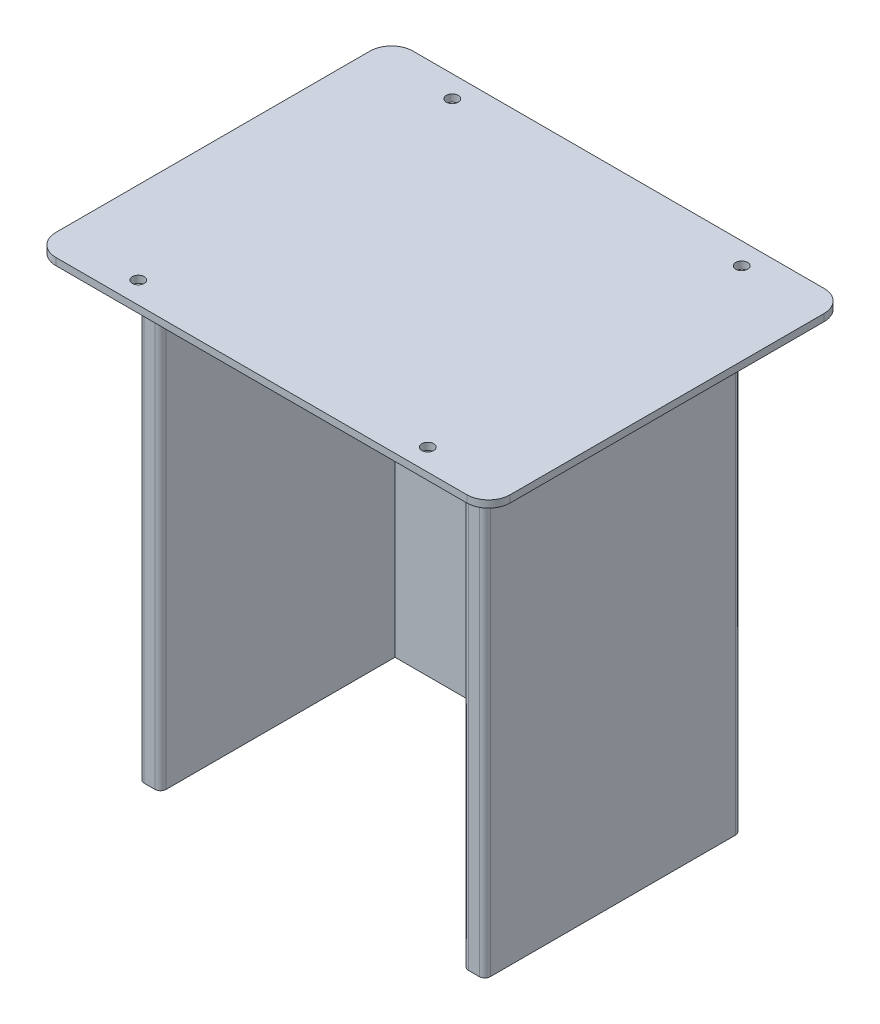
SolidWorks part; units mm, degrees
ref_plane "Front Plane" through (0, 0, 0) normal (0, 0, 1) x (1, 0, 0)
ref_plane "Top Plane" through (0, 0, 0) normal (0, 1, 0) x (1, 0, 0)
ref_plane "Right Plane" through (0, 0, 0) normal (1, 0, 0) x (0, 0, -1)
sketch "Sketch1" plane through (0, 0, 0) normal (0, 1, 0) x (1, 0, 0)
  line L1 (-99.9344, -82.55) -> (110.0102, -82.55)
  line L2 (-99.9344, -82.55) -> (-99.9344, 82.55)
  line L3 (-99.9344, 82.55) -> (110.0102, 82.55)
  line L4 (110.0102, -82.55) -> (110.0102, 82.55)
  point P0 (0, 0)
  dimension "D1" = 165.1
  dimension "D2" = 99.9344
  dimension "D3" = 82.55
  dimension "D4" = 209.9446
extrude "Boss-Extrude1" add sketch "Sketch1" along normal blind 3.302
hole_wizard "M5 Clearance Hole2" positions "Sketch10" profile "Sketch11" hole size "M5" standard "ANSI Metric" end condition up to next
sketch "Sketch10" plane through (0, 3.302, 0) normal (0, 1, 0) x (1, 0, 0)
  line L0 (5.0379, -82.55) -> (5.0379, 82.55) construction
  line L1 (-99.9344, -82.55) -> (110.0102, -82.55) construction
  line L2 (110.0102, 82.55) -> (-99.9344, 82.55) construction
  line L5 (100.0102, -72.55) -> (-89.9344, -72.55) construction
  line L6 (100.0102, -72.55) -> (100.0102, 72.55) construction
  line L7 (100.0102, 72.55) -> (-89.9344, 72.55) construction
  line L8 (-89.9344, -72.55) -> (-89.9344, 72.55) construction
  line L9 (100.0102, -72.55) -> (-89.9344, 72.55) construction
  line L10 (100.0102, 72.55) -> (-89.9344, -72.55) construction
  line L11 (110.0102, -82.55) -> (110.0102, 82.55) construction
  line L12 (-99.9344, 82.55) -> (-99.9344, -82.55) construction
  point P0 (71.9102, -72.55)
  point P7 (-61.8344, -72.55)
  point P9 (71.9102, 72.55)
  point P16 (-61.8344, 72.55)
  point P197 (71.8682, 72.55)
  point P198 (71.8682, 72.55)
  point P199 (0, 0)
  point P200 (0, 0)
  point P201 (0, 0)
  point P202 (0, 0)
  point P203 (0, 0)
  point P204 (0, 0)
  point P205 (0, 0)
  point P206 (0, 0)
  point P209 (0, 0)
  point P210 (0, 0)
  point P211 (0, 0)
  point P212 (0, 0)
  point P213 (0, 0)
  dimension "D1" = 10
  dimension "D2" = 10
  dimension "D3" = 10
  dimension "D4" = 38.1
  dimension "D5" = 38.1
  dimension "D6" = 10
sketch "Sketch11" plane through (71.9102, 3.302, 72.55) normal (1, 0, 0) x (0, 0, 1)
  line L0 (0, 0) -> (0, 3.302)
  line L1 (0, 3.302) -> (2.75, 3.302)
  line L2 (2.75, 3.302) -> (2.75, 0)
  line L5 (2.75, 0) -> (0, 0)
  line L11 (0, -6.35) -> (0, 107.95) construction
  dimension "Thru Hole Dia." = 5.5
  dimension "Thru Hole Depth" = 3.302
sketch "Sketch12" plane through (0, 0, 0) normal (0, -1, 0) x (1, 0, 0)
  line L0 (0, 82.55) -> (0, 59.25) construction
  line L2 (-99.9344, 0) -> (-70.043, 0) construction
  line L3 (-99.9344, -82.55) -> (-99.9344, 82.55) construction
  line L4 (0, -82.55) -> (0, -59.25) construction
  line L6 (-75.0051, 80.5434) -> (-75.0051, 75.8444) construction
  line L12 (85.0051, 59.25) -> (-75.0051, 59.25)
  line L13 (85.0051, 59.25) -> (85.0051, -59.25)
  line L14 (85.0051, -59.25) -> (-75.0051, -59.25)
  line L15 (-75.0051, 59.25) -> (-75.0051, -59.25)
  line L16 (-75.0051, 59.25) -> (-64.8451, 59.25)
  line L17 (85.0051, 59.25) -> (74.9209, 59.25)
  line L18 (-64.8451, -59.25) -> (-64.8451, -49.09) construction
  line L19 (74.9209, -59.25) -> (74.9209, -49.09) construction
  line L20 (-64.8451, 59.25) -> (-64.8451, -49.09)
  line L21 (-64.8451, -49.09) -> (74.9209, -49.09)
  line L22 (74.9209, -49.09) -> (74.9209, 59.25)
  line L26 (85.0051, 64.5668) -> (85.0051, 69.2658) construction
  line M13 (110.0102, -82.55) -> (110.0102, 82.55)
fillet "Fillet1" radius 10 4 edges at (-99.9344, 1.651, -82.55) (110.0102, 1.651, -82.55) (110.0102, 1.651, 82.55) (-99.9344, 1.651, 82.55)
extrude "Boss-Extrude2" add sketch "Sketch12" along normal blind 210 contours L22 L21 L20 L12 L15 L14 M13
sketch "Sketch21" plane through (0, -210, 0) normal (0, -1, 0) x (1, 0, 0)
  line L0 (-69.9251, 59.25) -> (-69.9251, -59.25) construction
  line L1 (-64.8451, 59.25) -> (-75.0051, 59.25) construction
  line L2 (85.0051, -59.25) -> (-75.0051, -59.25) construction
  line L3 (79.963, 59.25) -> (79.963, -59.25) construction
  line L4 (85.0051, 59.25) -> (74.9209, 59.25) construction
  line L5 (85.0051, -59.25) -> (-75.0051, -59.25) construction
  line L6 (-75.0051, -59.25) -> (-75.0051, -54.17) construction
  line L7 (-75.0051, 59.25) -> (-75.0051, -59.25) construction
  line L8 (-75.0051, -54.17) -> (94.9949, -54.17) construction
hole_wizard "1/8 (0.1250) Dowel Hole1" positions "Sketch22" profile "Sketch24" hole size "1/8" standard "ANSI Inch"
sketch "Sketch22" plane through (0, -210, 0) normal (0, -1, 0) x (-1, 0, 0)
  line L0 (69.9251, -59.25) -> (69.9251, 59.25) construction
  line L1 (75.0051, 54.17) -> (-94.9949, 54.17) construction
  line L2 (-79.963, -59.25) -> (-79.963, 59.25) construction
  point P0 (69.9251, -21.15)
  point P4 (69.9251, 21.15)
  point P6 (36.9051, 54.17)
  point P10 (-56.8949, 54.17)
  point P12 (-79.963, 21.15)
  point P16 (-79.963, -21.15)
  dimension "D1" = 38.1
  dimension "D2" = 38.1
  dimension "D3" = 38.1
  dimension "D4" = 38.1
  dimension "D5" = 38.1
  dimension "D6" = 38.1
sketch "Sketch24" plane through (-69.9251, -210, 21.15) normal (1, 0, 0) x (0, 0, -1)
  line L0 (0, 0) -> (0, 26.3539)
  line L1 (0, 26.3539) -> (1.5875, 25.4)
  line L2 (1.5875, 25.4) -> (1.5875, 0)
  line L5 (1.5875, 0) -> (0, 0)
  line L10 (0, 26.3539) -> (-1.5875, 25.4) construction
  line L11 (0, -6.35) -> (0, 107.95) construction
  dimension "Hole Dia." = 3.175
  dimension "Hole Depth" = 25.4
  dimension "Drill Angle" = 118
sketch "Sketch25" plane through (0, -210, 0) normal (0, -1, 0) x (-1, 0, 0)
  line L0 (75.0051, 59.25) -> (-85.0051, 59.25)
  line L1 (-85.0051, 59.25) -> (-85.0051, 57.98)
  line L3 (-85.0051, 57.98) -> (75.0051, 57.98)
  line L4 (75.0051, -59.25) -> (75.0051, 59.25) construction
  line L5 (75.0051, 57.98) -> (75.0051, 59.25)
  line L6 (-85.0051, -59.25) -> (-85.0051, 59.25) construction
  dimension "D1" = 1.27
extrude "Cut-Extrude1" cut sketch "Sketch25" against normal up to surface (210 mm away) up to face at (5.019, 0, 2.54)
sketch "Sketch26" plane through (0, -210, 0) normal (0, -1, 0) x (-1, 0, 0)
  line L0 (75.0051, 57.98) -> (-85.0051, 57.98)
  line L1 (-85.0051, 57.98) -> (-85.0051, 59.1378)
  line L3 (-85.0051, 59.1378) -> (75.0051, 59.1378)
  line L4 (75.0051, 59.1378) -> (75.0051, 57.98)
  line L6 (-85.0051, -59.25) -> (-85.0051, 57.98) construction
  dimension "D1" = 1.1578
extrude "Boss-Extrude3" add sketch "Sketch26" against normal up to surface (210 mm away) up to face at (5.019, 0, 2.8575)
fillet "Fillet2" radius 2.54 6 edges at (-75.0051, -105, -59.1378) (85.0051, -105, -59.1378) (74.9209, -105, 59.25) (-64.8451, -105, 59.25) (-75.0051, -105, 59.25) (85.0051, -105, 59.25)
